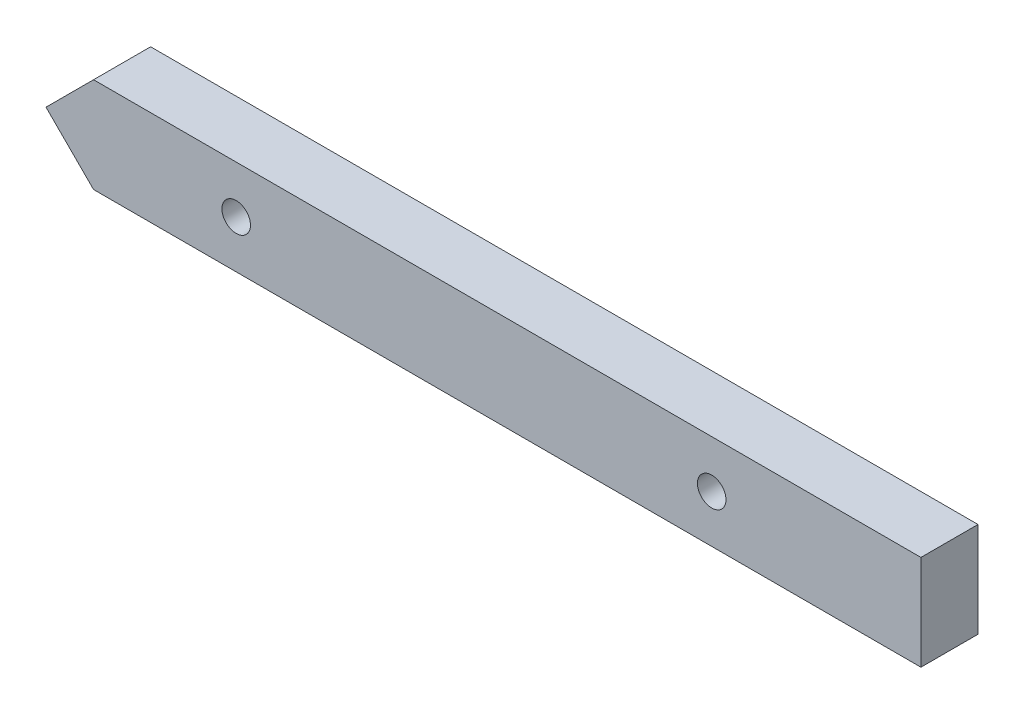
SolidWorks part; units mm, degrees
ref_plane "Plan de face" through (0, 0, 0) normal (0, 0, 1) x (1, 0, 0)
ref_plane "Plan de dessus" through (0, 0, 0) normal (0, 1, 0) x (1, 0, 0)
ref_plane "Plan de droite" through (0, 0, 0) normal (1, 0, 0) x (0, 0, -1)
sketch "Esquisse1" plane through (0, 0, 0) normal (0, 0, 1) x (1, 0, 0)
  line L1 (-46, 5) -> (46, 5)
  line L2 (-46, 5) -> (-46, -5)
  line L3 (-46, -5) -> (46, -5)
  line L4 (46, 5) -> (46, -5)
  point P7 (-5.9436, -2.2982)
  dimension "D1" = 92
  dimension "D2" = 10
  dimension "D3" = 5
  dimension "D4" = 46
extrude "Boss.-Extru.1" add sketch "Esquisse1" along normal blind 6
sketch "Esquisse2" plane through (0, 0, 6) normal (0, 0, 1) x (1, 0, 0)
  line L0 (-46, -5) -> (-46, 0)
  line L1 (-46, 5) -> (-46, -5) construction
  line L3 (-46, 0) -> (-41, -5)
  line L4 (-46, -5) -> (46, -5) construction
  line L5 (-41, -5) -> (-46, -5)
  dimension "D2" = 5
extrude "Enlèv. mat.-Extru.1" cut sketch "Esquisse2" against normal blind 6
sketch "Esquisse3" plane through (0, 0, 6) normal (0, 0, 1) x (1, 0, 0)
  line L0 (-46, 0) -> (-41, 5)
  line L1 (46, 5) -> (-46, 5) construction
  line L2 (-41, 5) -> (-46, 5)
  line L3 (-46, 5) -> (-46, 0)
  dimension "D1" = 5
extrude "Enlèv. mat.-Extru.2" cut sketch "Esquisse3" against normal blind 6
sketch "Esquisse4" plane through (0, 0, 6) normal (0, 0, 1) x (1, 0, 0)
  circle A0 centre (-26, 0) radius 1.5
  circle A1 centre (24, 0) radius 1.5
  dimension "D1" = 3
  dimension "D2" = 3
  dimension "D3" = 50
  dimension "D4" = 20
extrude "Enlèv. mat.-Extru.3" cut sketch "Esquisse4" against normal blind 6
equation "\"D3@Esquisse1\"=\"D2@Esquisse1\"/2"
equation "\"D4@Esquisse1\"=\"D1@Esquisse1\"/2"
